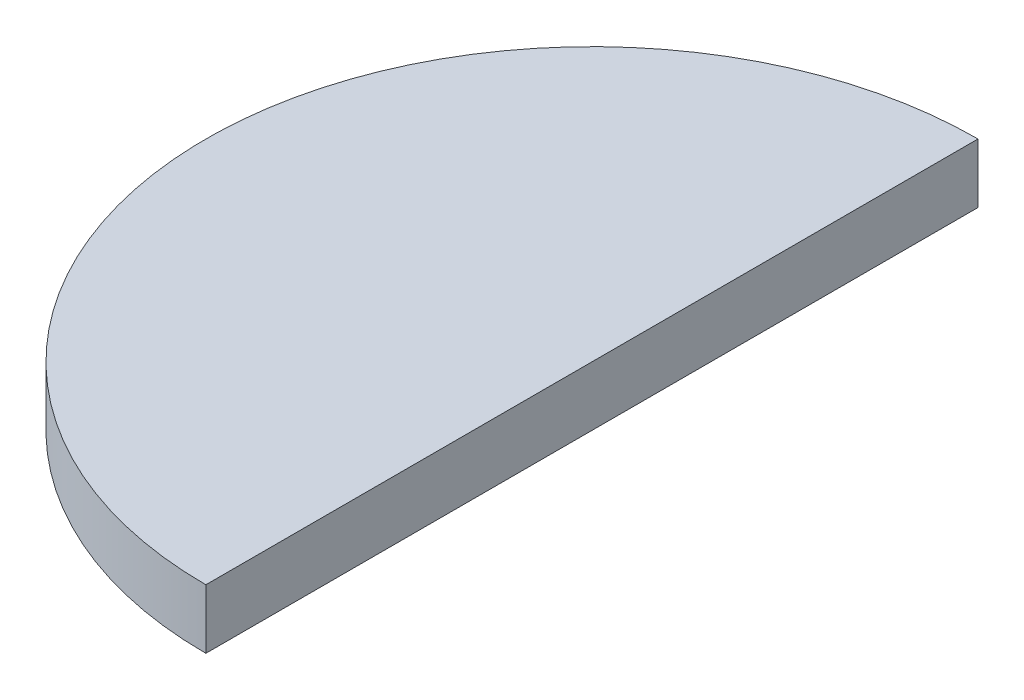
SolidWorks part; units mm, degrees
ref_plane "Ebene vorne" through (0, 0, 0) normal (0, 0, 1) x (1, 0, 0)
ref_plane "Ebene oben" through (0, 0, 0) normal (0, 1, 0) x (1, 0, 0)
ref_plane "Ebene rechts" through (0, 0, 0) normal (1, 0, 0) x (0, 0, -1)
sketch "Skizze1" plane through (0, 0, 0) normal (0, 1, 0) x (1, 0, 0)
  line L0 (0, 0) -> (0, -65)
  arc A1 (0, -65) -> (0, 0) centre (0, -32.5) cw
  dimension "D1" = 65
extrude "Aufsatz-Linear austragen1" add sketch "Skizze1" along normal blind 5
